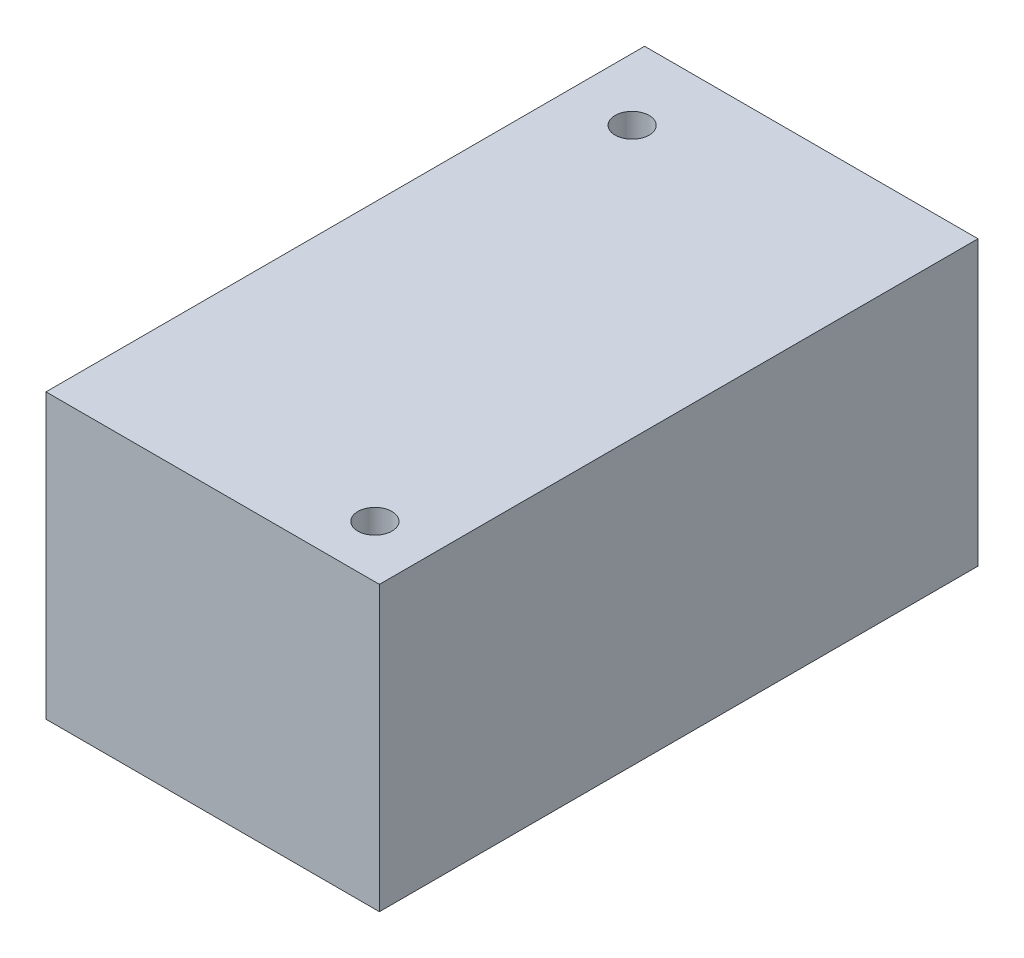
SolidWorks part; units mm, degrees
ref_plane "Front Plane" through (0, 0, 0) normal (0, 0, 1) x (1, 0, 0)
ref_plane "Top Plane" through (0, 0, 0) normal (0, 1, 0) x (1, 0, 0)
ref_plane "Right Plane" through (0, 0, 0) normal (1, 0, 0) x (0, 0, -1)
sketch "Sketch1" plane through (0, 0, 0) normal (0, 0, 1) x (1, 0, 0)
  line L1 (-63.5, 45) -> (63.5, 45)
  line L2 (-63.5, 45) -> (-63.5, -45)
  line L3 (-63.5, -45) -> (63.5, -45)
  line L4 (63.5, 45) -> (63.5, -45)
  line L5 (-63.5, 45) -> (63.5, -45) construction
  line L6 (-63.5, -45) -> (63.5, 45) construction
  point P0 (0, 0)
  dimension "D1" = 127
  dimension "D2" = 90
extrude "Boss-Extrude1" add sketch "Sketch1" along normal blind 228
sketch "Sketch2" plane through (0, 45, 0) normal (0, 1, 0) x (1, 0, 0)
  circle A0 centre (-39.8023, -28.442) radius 6.5
  circle A1 centre (41.8435, -208.0628) radius 6.5
  dimension "D1" = 13
  dimension "D2" = 13
extrude "Cut-Extrude1" cut sketch "Sketch2" against normal blind 228 contours A1 | A0
sketch "Sketch3" plane through (0, 45, 0) normal (0, 1, 0) x (1, 0, 0)
  line L1 (-63.5, -228) -> (63.5, -228)
  line L2 (-63.5, -228) -> (-63.5, 0)
  line L3 (-63.5, 0) -> (63.5, 0)
  line L4 (63.5, -228) -> (63.5, 0)
  circle A0 centre (-39.8023, -28.442) radius 6.5
  circle A1 centre (41.8435, -208.0628) radius 6.5
extrude "Boss-Extrude2" add sketch "Sketch3" along normal blind 18
